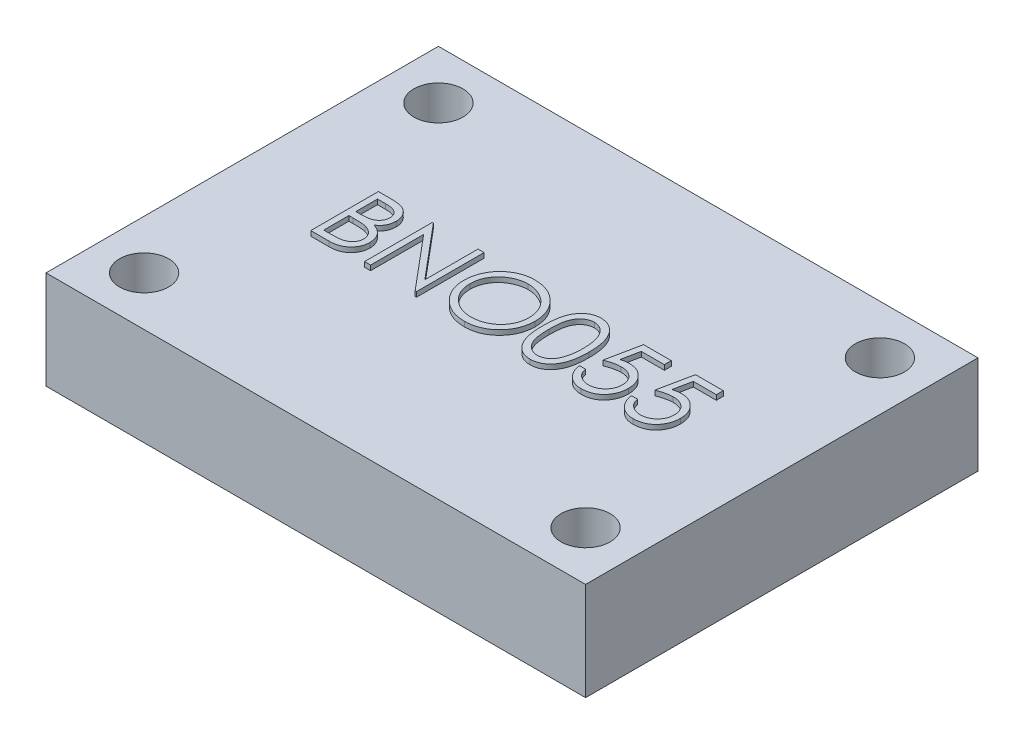
SolidWorks part; units mm, degrees
ref_plane "Front Plane" through (0, 0, 0) normal (0, 0, 1) x (1, 0, 0)
ref_plane "Top Plane" through (0, 0, 0) normal (0, 1, 0) x (1, 0, 0)
ref_plane "Right Plane" through (0, 0, 0) normal (1, 0, 0) x (0, 0, -1)
sketch "Sketch1" plane through (0, 0, 0) normal (0, 1, 0) x (1, 0, 0)
  line L1 (-13.97, 10.16) -> (13.97, 10.16)
  line L2 (-13.97, 10.16) -> (-13.97, -10.16)
  line L3 (-13.97, -10.16) -> (13.97, -10.16)
  line L4 (13.97, 10.16) -> (13.97, -10.16)
  line L5 (-13.97, 10.16) -> (13.97, -10.16) construction
  line L6 (-13.97, -10.16) -> (13.97, 10.16) construction
  circle A0 centre (-11.43, 7.62) radius 1.27
  circle A1 centre (11.43, 7.62) radius 1.27
  circle A2 centre (11.43, -7.62) radius 1.27
  circle A3 centre (-11.43, -7.62) radius 1.27
  point P0 (0, 0)
  dimension "D3" = 2.54
  dimension "D8" = 2.54
  dimension "D10" = 22.86
  dimension "D1" = 20.32
  dimension "D2" = 27.94
  dimension "D4" = 2.54
  dimension "D5" = 2.54
  dimension "D9" = 2.54
  dimension "D6" = 2
  dimension "D7" = 2
extrude "Boss-Extrude1" add sketch "Sketch1" against normal blind 5.08
sketch "Sketch2" plane through (0, 0, 0) normal (0, 1, 0) x (1, 0, 0)
  text T0 "BNO055"
extrude "Boss-Extrude2" add sketch "Sketch2" along normal blind 0.254
